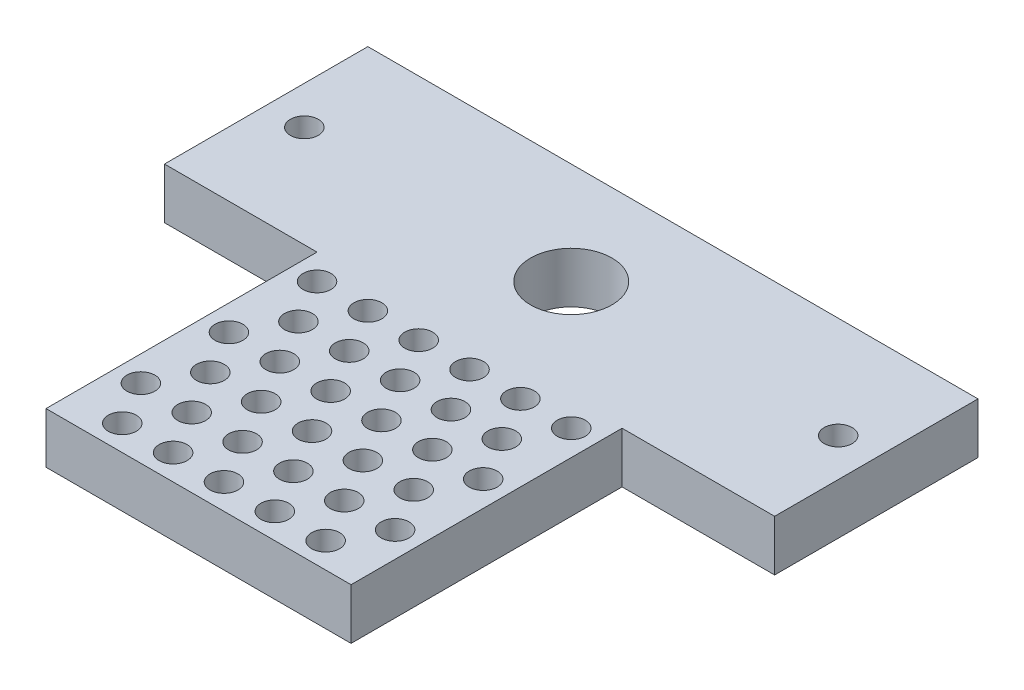
SolidWorks part; units mm, degrees
ref_plane "Front Plane" through (0, 0, 0) normal (0, 0, 1) x (1, 0, 0)
ref_plane "Top Plane" through (0, 0, 0) normal (0, 1, 0) x (1, 0, 0)
ref_plane "Right Plane" through (0, 0, 0) normal (1, 0, 0) x (0, 0, -1)
sketch "elec_row1" plane through (0, 0, 0) normal (0, 1, 0) x (1, 0, 0)
  circle A0 centre (-22.2907, 0) radius 0.1397
  circle A1 centre (-21.7827, 0) radius 0.1397
  circle A2 centre (-21.2747, 0) radius 0.1397
  circle A3 centre (-20.7667, 0) radius 0.1397
  circle A4 centre (-20.2587, 0) radius 0.1397
sketch "elec_row2" plane through (0, 0, 0) normal (0, 1, 0) x (1, 0, 0)
  circle A0 centre (-22.0367, 0.4399) radius 0.1397
  circle A1 centre (-21.5287, 0.4399) radius 0.1397
  circle A2 centre (-21.0207, 0.4399) radius 0.1397
  circle A3 centre (-20.5127, 0.4399) radius 0.1397
  circle A4 centre (-20.0047, 0.4399) radius 0.1397
  dimension "D2" = 0.508
  dimension "D3" = 0.508
  dimension "D4" = 0.508
sketch "elec_row3" plane through (0, 0, 0) normal (0, 1, 0) x (1, 0, 0)
  circle A0 centre (-22.2907, 0.8799) radius 0.1397
  circle A1 centre (-21.7827, 0.8799) radius 0.1397
  circle A2 centre (-21.2747, 0.8799) radius 0.1397
  circle A3 centre (-20.7667, 0.8799) radius 0.1397
  circle A4 centre (-20.2587, 0.8799) radius 0.1397
  dimension "D2" = 0.508
  dimension "D3" = 0.508
sketch "elec_row4" plane through (0, 0, 0) normal (0, 1, 0) x (1, 0, 0)
  circle A0 centre (-22.0367, 1.3198) radius 0.1397
  circle A1 centre (-21.5287, 1.3198) radius 0.1397
  circle A2 centre (-21.0207, 1.3198) radius 0.1397
  circle A3 centre (-20.5127, 1.3198) radius 0.1397
  circle A4 centre (-20.0047, 1.3198) radius 0.1397
  dimension "D2" = 0.508
  dimension "D3" = 0.508
sketch "elec_row5" plane through (0, 0, 0) normal (0, 1, 0) x (1, 0, 0)
  circle A0 centre (-22.2907, 1.7598) radius 0.1397
  circle A1 centre (-21.7827, 1.7598) radius 0.1397
  circle A2 centre (-21.2747, 1.7598) radius 0.1397
  circle A3 centre (-20.7667, 1.7598) radius 0.1397
  circle A4 centre (-20.2587, 1.7598) radius 0.1397
  dimension "D2" = 0.508
  dimension "D3" = 0.508
sketch "elec_misc1" plane through (0, 0, 0) normal (0, 1, 0) x (1, 0, 0)
  circle A0 centre (-22.5447, 1.3198) radius 0.1397
  dimension "D1" = 0.508
  dimension "D2" = 0.508
  dimension "D3" = 0.508
sketch "elec_misc2" plane through (0, 0, 0) normal (0, 1, 0) x (1, 0, 0)
  circle A0 centre (-22.5447, 0.4399) radius 0.1397
  dimension "D1" = 0.508
  dimension "D2" = 0.508
sketch "elec_row6" plane through (0, 0, 0) normal (0, 1, 0) x (1, 0, 0)
  circle A0 centre (-20.0047, 2.1997) radius 0.1397
  circle A1 centre (-20.5127, 2.1997) radius 0.1397
  circle A2 centre (-21.0207, 2.1997) radius 0.1397
  circle A3 centre (-21.5287, 2.1997) radius 0.1397
  circle A4 centre (-22.0367, 2.1997) radius 0.1397
  circle A5 centre (-22.5447, 2.1997) radius 0.1397
  dimension "D1" = 0.508
  dimension "D3" = 0.508
  dimension "D2" = 6
sketch "elec_bounding" plane through (0, 0, 0) normal (0, 1, 0) x (1, 0, 0)
  line L1 (-22.7987, 2.4537) -> (-19.7507, 2.4537)
  line L2 (-22.7987, 2.4537) -> (-22.7987, -0.254)
  line L3 (-22.7987, -0.254) -> (-19.7507, -0.254)
  line L4 (-19.7507, 2.4537) -> (-19.7507, -0.254)
  dimension "D1" = 0.254
  dimension "D2" = 0.254
  dimension "D3" = 0.254
  dimension "D4" = 0.254
  dimension "D5" = 0.254
sketch "shuttle" plane through (0, 0, 0) normal (0, 1, 0) x (1, 0, 0)
  line L0 (-22.7987, 2.4537) -> (-22.7987, -0.254) construction
  line L1 (-24.3227, 2.4537) -> (-18.2267, 2.4537)
  line L2 (-24.3227, 2.4537) -> (-24.3227, 4.4857)
  line L3 (-24.3227, 4.4857) -> (-18.2267, 4.4857)
  line L4 (-18.2267, 2.4537) -> (-18.2267, 4.4857)
  line L5 (-19.7507, 2.4537) -> (-19.7507, -0.254) construction
  dimension "D1" = 2.032
  dimension "D2" = 1.524
  dimension "D3" = 1.524
sketch "drive_screw" plane through (0, 0, 0) normal (0, 1, 0) x (1, 0, 0)
  line L0 (-19.7507, 2.4537) -> (-19.7507, -0.254) construction
  line L2 (-22.7987, 2.4537) -> (-22.7987, -0.254) construction
  line L3 (-24.3227, 2.4537) -> (-18.2267, 2.4537) construction
  circle A0 centre (-21.2747, 3.4697) radius 0.4064
  dimension "D1" = 1.524
  dimension "D2" = 1.524
  dimension "D3" = 1.016
sketch "guide_holes" plane through (0, 0, 0) normal (0, 1, 0) x (1, 0, 0)
  line L0 (-24.3227, 2.4537) -> (-24.3227, 4.4857) construction
  circle A0 centre (-23.9417, 3.4697) radius 0.1397
  circle A1 centre (-18.6077, 3.4697) radius 0.1397
  dimension "D1" = 0.381
  dimension "D2" = 2
extrude "shuttle_extr" add sketch "shuttle" against normal blind 0.508
extrude "elec_bounding_extr" add sketch "elec_bounding" against normal blind 0.508
extrude "elec_row1_extr" cut sketch "elec_row1" against normal blind 0.508
extrude "elec_row2_extr" cut sketch "elec_row2" against normal blind 0.508
extrude "elec_row3_extr" cut sketch "elec_row3" against normal blind 0.508
extrude "elec_row4_extr" cut sketch "elec_row4" against normal blind 0.508
extrude "elec_row5_extr" cut sketch "elec_row5" against normal blind 0.508
extrude "elec_misc1_extr" cut sketch "elec_misc1" against normal blind 0.508
extrude "elec_misc2_extr" cut sketch "elec_misc2" against normal blind 0.508
extrude "elec_row6_extr" cut sketch "elec_row6" against normal blind 0.508
extrude "drive_screw_extr" cut sketch "drive_screw" against normal blind 0.508
extrude "guide_holes_extr" cut sketch "guide_holes" against normal blind 0.508
sketch "Sketch18" plane through (0, 0, 0) normal (0, 1, 0) x (1, 0, 0)
  circle A0 centre (-18.7408, -0.1252) radius 0.1397
  circle A1 centre (-18.2328, -0.1252) radius 0.1397
  circle A2 centre (-17.7248, -0.1252) radius 0.1397
  circle A3 centre (-17.2168, -0.1252) radius 0.1397
  circle A4 centre (-16.7088, -0.1252) radius 0.1397
  circle A5 centre (-16.2008, -0.1252) radius 0.1397
  circle A6 centre (-15.6928, -0.1252) radius 0.1397
  circle A7 centre (-15.1848, -0.1252) radius 0.1397
  circle A8 centre (-18.2328, 0.3828) radius 0.1397
  circle A9 centre (-17.7248, 0.3828) radius 0.1397
  circle A10 centre (-17.2168, 0.3828) radius 0.1397
  circle A11 centre (-16.7088, 0.3828) radius 0.1397
  circle A12 centre (-16.2008, 0.3828) radius 0.1397
  circle A13 centre (-15.6928, 0.3828) radius 0.1397
  circle A14 centre (-15.1848, 0.3828) radius 0.1397
  circle A15 centre (-18.2328, 0.8908) radius 0.1397
  circle A16 centre (-17.7248, 0.8908) radius 0.1397
  circle A17 centre (-17.2168, 0.8908) radius 0.1397
  circle A18 centre (-16.7088, 0.8908) radius 0.1397
  circle A19 centre (-16.2008, 0.8908) radius 0.1397
  circle A20 centre (-15.6928, 0.8908) radius 0.1397
  circle A21 centre (-15.1848, 0.8908) radius 0.1397
  circle A22 centre (-18.2328, 1.3988) radius 0.1397
  circle A23 centre (-17.7248, 1.3988) radius 0.1397
  circle A24 centre (-17.2168, 1.3988) radius 0.1397
  circle A25 centre (-16.7088, 1.3988) radius 0.1397
  circle A26 centre (-16.2008, 1.3988) radius 0.1397
  circle A27 centre (-15.6928, 1.3988) radius 0.1397
  circle A28 centre (-15.1848, 1.3988) radius 0.1397
  circle A29 centre (-18.7408, 0.3828) radius 0.1397
  circle A30 centre (-18.7408, 0.8908) radius 0.1397
  circle A31 centre (-18.7408, 1.3988) radius 0.1397
  dimension "D1" = 8
  dimension "D2" = 4
